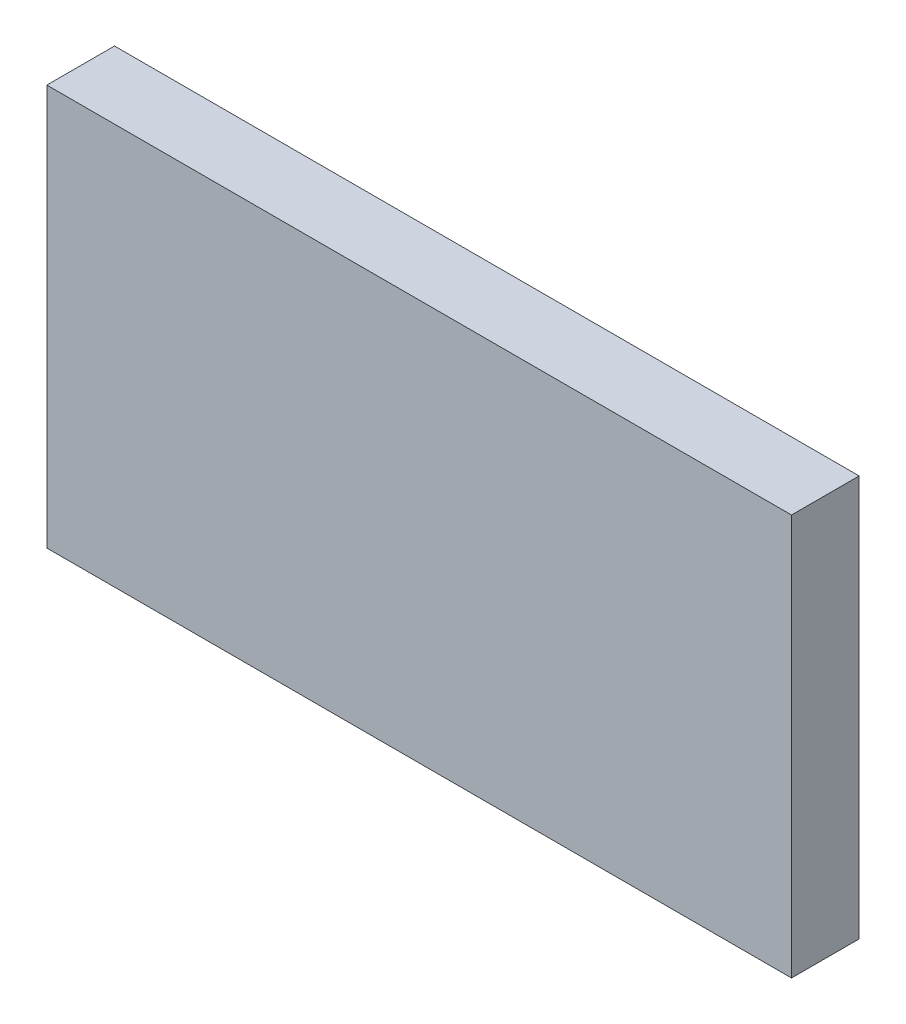
SolidWorks part; units mm, degrees
ref_plane "Front Plane" through (0, 0, 0) normal (0, 0, 1) x (1, 0, 0)
ref_plane "Top Plane" through (0, 0, 0) normal (0, 1, 0) x (1, 0, 0)
ref_plane "Right Plane" through (0, 0, 0) normal (1, 0, 0) x (0, 0, -1)
sketch "Sketch1" plane through (0, 0, 0) normal (0, 0, 1) x (1, 0, 0)
  line L4 (-33.02, 17.78) -> (0, 17.78)
  line L5 (-33.02, 17.78) -> (-33.02, 0)
  line L6 (-33.02, 0) -> (0, 0)
  line L7 (0, 17.78) -> (0, 0)
  point P5 (0, 8.89)
  dimension "D1" = 0
extrude "Boss-Extrude1" add sketch "Sketch1" along normal blind 3
